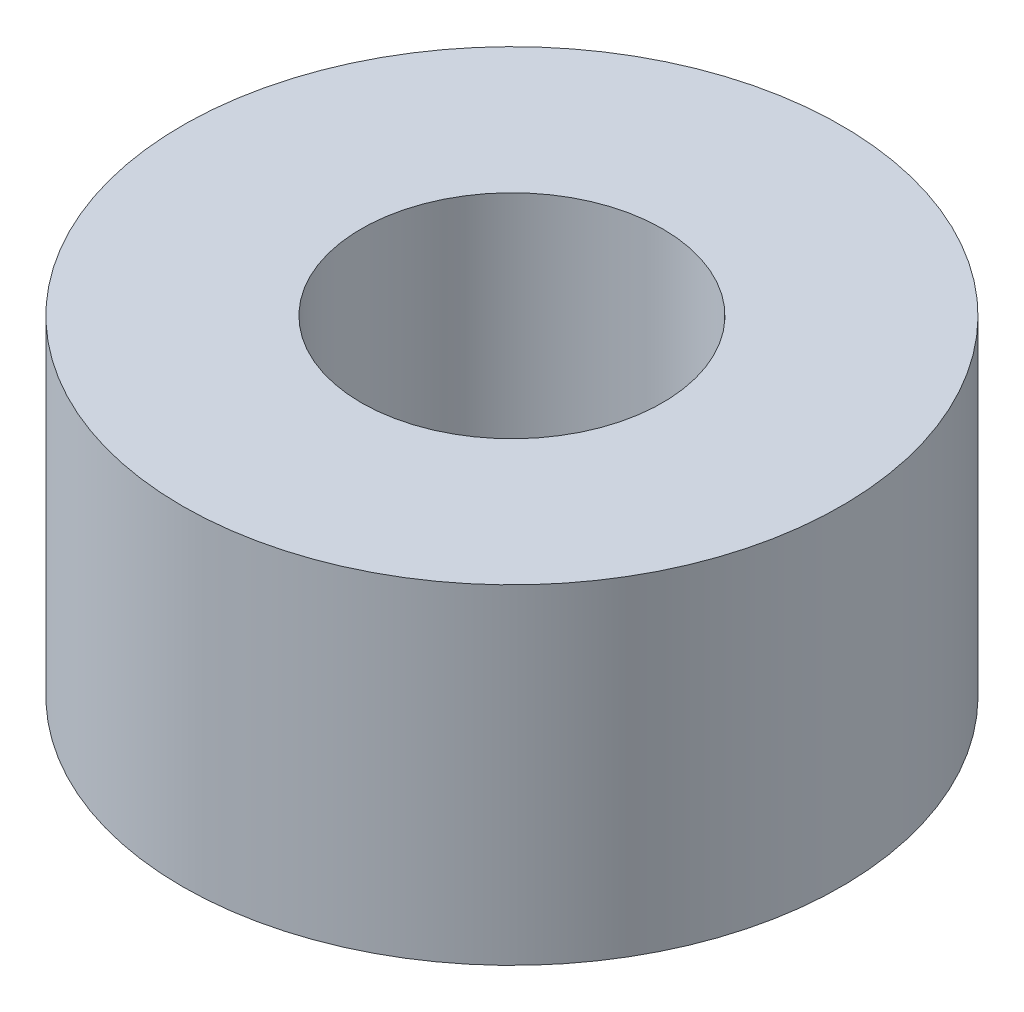
SolidWorks part; units mm, degrees
ref_plane "Front Plane" through (0, 0, 0) normal (0, 0, 1) x (1, 0, 0)
ref_plane "Top Plane" through (0, 0, 0) normal (0, 1, 0) x (1, 0, 0)
ref_plane "Right Plane" through (0, 0, 0) normal (1, 0, 0) x (0, 0, -1)
sketch "Sketch1" plane through (0, 0, 0) normal (0, 1, 0) x (1, 0, 0)
  circle A0 centre (0, 0) radius 3.5
  circle A1 centre (0, 0) radius 1.6
  dimension "D1" = 7
  dimension "D2" = 3.2
extrude "Boss-Extrude1" add sketch "Sketch1" along normal blind 3.5
